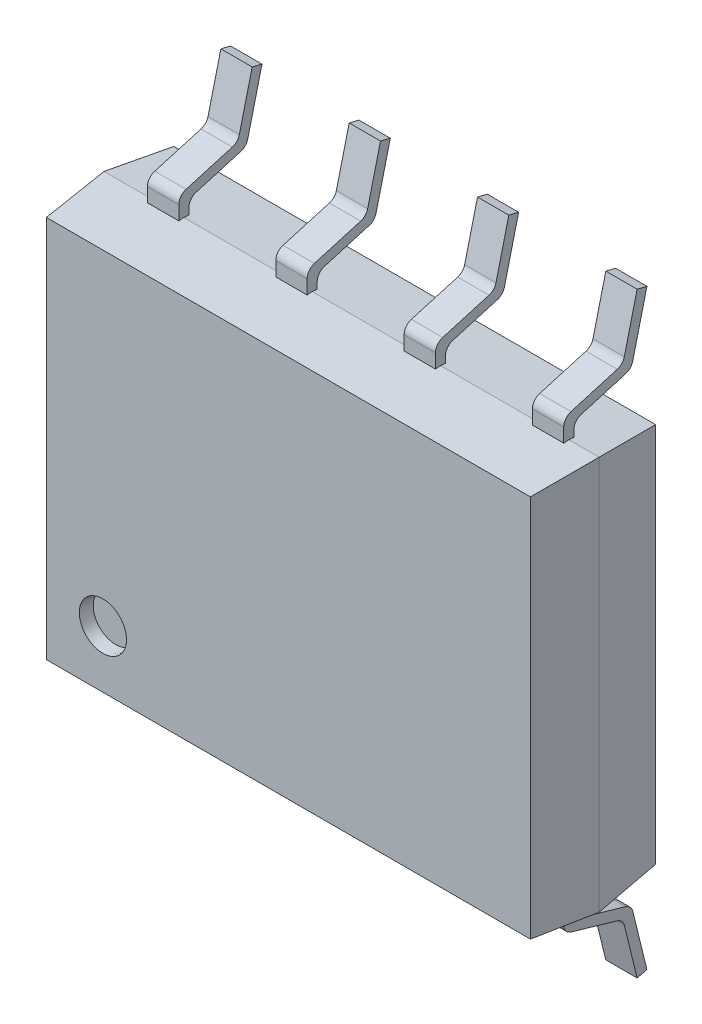
SolidWorks part; units mm, degrees
ref_plane "Front Plane" through (0, 0, 0) normal (0, 0, 1) x (1, 0, 0)
ref_plane "Top Plane" through (0, 0, 0) normal (0, 1, 0) x (1, 0, 0)
ref_plane "Right Plane" through (0, 0, 0) normal (1, 0, 0) x (0, 0, -1)
sketch "Sketch1" plane through (0, 0, 0) normal (0, 0, 1) x (1, 0, 0)
  line L1 (0, 0) -> (4.9, 0)
  line L2 (0, 0) -> (0, 3.9)
  line L3 (0, 3.9) -> (4.9, 3.9)
  line L4 (4.9, 0) -> (4.9, 3.9)
  dimension "D1" = 4.9
  dimension "D2" = 3.9
extrude "Boss-Extrude1" add sketch "Sketch1" along normal blind 0.625 draft 5
sketch "Sketch2" plane through (0, 0, 0) normal (0, 0, -1) x (-1, 0, 0)
  line L1 (-4.9, 3.9) -> (0, 3.9)
  line L2 (-4.9, 3.9) -> (-4.9, 0)
  line L3 (-4.9, 0) -> (0, 0)
  line L4 (0, 3.9) -> (0, 0)
extrude "Boss-Extrude2" add sketch "Sketch2" along normal blind 0.625 draft 6 separate body
sketch "Sketch3" plane through (0, 0, 0.625) normal (0, 0, 1) x (1, 0, 0)
  circle A0 centre (0.6138, 0.6221) radius 0.2336
extrude "Cut-Extrude1" cut sketch "Sketch3" against normal blind 0.127 draft 5
ref_plane "Plane1" through (0.635, 0, 0) normal (1, 0, 0) x (0, 0, -1)
sketch "Sketch4" plane through (0.635, 0, 0) normal (1, 0, 0) x (0, 0, -1)
  line L0 (0, 0) -> (0, -0.2721)
  line L1 (0, -0.2721) -> (0.5773, -0.44)
  line L2 (0.5773, -0.44) -> (0.725, -1.04)
  line L3 (0.625, 3.8343) -> (0.625, 0.0657) construction
  dimension "D1" = 0.6
  dimension "D3" = 1.04
  dimension "D4" = 0.1
extrude "Extrude-Thin1" add sketch "Sketch4" along normal mid plane 0.31 separate body thin
pattern_linear "LPattern4" count 4 spacing 1.27 along (1, 0, 0) of "Extrude-Thin1"
fillet "Fillet1" radius 0.1 4 edges at (0.635, -0.48, -0.5357) (0.635, -0.4, -0.619) (0.635, -0.2346, -0.05) (0.635, -0.3096, 0.05)
ref_plane "Plane3" through (0, 1.9, 0) normal (0, 1, 0) x (1, 0, 0)
fillet "Fillet2" radius 0.1 4 edges at (1.905, -0.4, -0.619) (1.905, -0.2346, -0.05) (1.905, -0.48, -0.5357) (1.905, -0.3096, 0.05)
fillet "Fillet3" radius 0.1 4 edges at (3.175, -0.48, -0.5357) (3.175, -0.3096, 0.05) (3.175, -0.4, -0.619) (3.175, -0.2346, -0.05)
fillet "Fillet4" radius 0.1 4 edges at (4.445, -0.4, -0.619) (4.445, -0.2346, -0.05) (4.445, -0.48, -0.5357) (4.445, -0.3096, 0.05)
mirror "Mirror3" about plane through (0, 1.9, 0) normal (0, 1, 0) of "Fillet4", "LPattern4", "Fillet2", "Fillet3", "Fillet1", "Extrude-Thin1"
